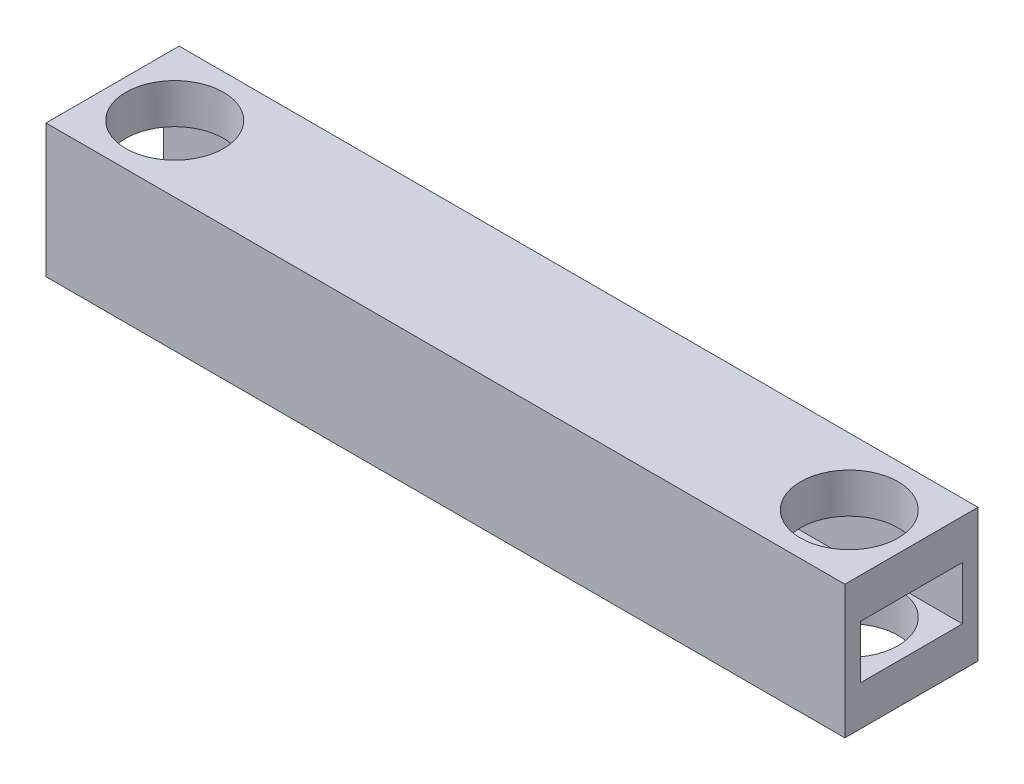
SolidWorks part; units mm, degrees
ref_plane "Front Plane" through (0, 0, 0) normal (0, 0, 1) x (1, 0, 0)
ref_plane "Top Plane" through (0, 0, 0) normal (0, 1, 0) x (1, 0, 0)
ref_plane "Right Plane" through (0, 0, 0) normal (1, 0, 0) x (0, 0, -1)
sketch "Sketch1" plane through (0, 0, 0) normal (0, 0, 1) x (1, 0, 0)
  line L1 (-54.7159, 19.517) -> (125.2841, 19.517)
  line L2 (-54.7159, 19.517) -> (-54.7159, -10.483)
  line L3 (-54.7159, -10.483) -> (125.2841, -10.483)
  line L4 (125.2841, 19.517) -> (125.2841, -10.483)
  dimension "D1" = 30
  dimension "D2" = 180
extrude "Boss-Extrude1" add sketch "Sketch1" along normal blind 30
sketch "Sketch2" plane through (0, 19.517, 0) normal (0, 1, 0) x (1, 0, 0)
  line L0 (125.2841, 0) -> (-54.7159, 0) construction
  line L1 (-54.7159, -30) -> (-54.7159, 0) construction
  circle A0 centre (-40.7159, -15) radius 11
  dimension "D1" = 22
  dimension "D2" = 15
  dimension "D3" = 14
extrude "Cut-Extrude1" cut sketch "Sketch2" against normal through all both and the other way through all
sketch "Sketch3" plane through (-54.7159, 0, 0) normal (-1, 0, 0) x (0, 0, 1)
  line L0 (30, 19.517) -> (0, 19.517) construction
  line L1 (3.5, 10.517) -> (26.5, 10.517)
  line L2 (3.5, 10.517) -> (3.5, -1.483)
  line L3 (3.5, -1.483) -> (26.5, -1.483)
  line L4 (26.5, 10.517) -> (26.5, -1.483)
  line L5 (0, 19.517) -> (0, -10.483) construction
  line L6 (30, -10.483) -> (0, -10.483) construction
  dimension "D1" = 9
  dimension "D2" = 23
  dimension "D3" = 9
  dimension "D4" = 3.5
extrude "Cut-Extrude2" cut sketch "Sketch3" against normal through all both
sketch "Sketch6" plane through (0, 19.517, 0) normal (0, 1, 0) x (1, 0, 0)
  line L0 (125.2841, -30) -> (125.2841, 0) construction
  line L1 (125.2841, 0) -> (-54.7159, 0) construction
  circle A0 centre (111.2841, -15) radius 11
  dimension "D1" = 22
  dimension "D2" = 14
  dimension "D3" = 15
extrude "Cut-Extrude5" cut sketch "Sketch6" against normal through all both and the other way through all
